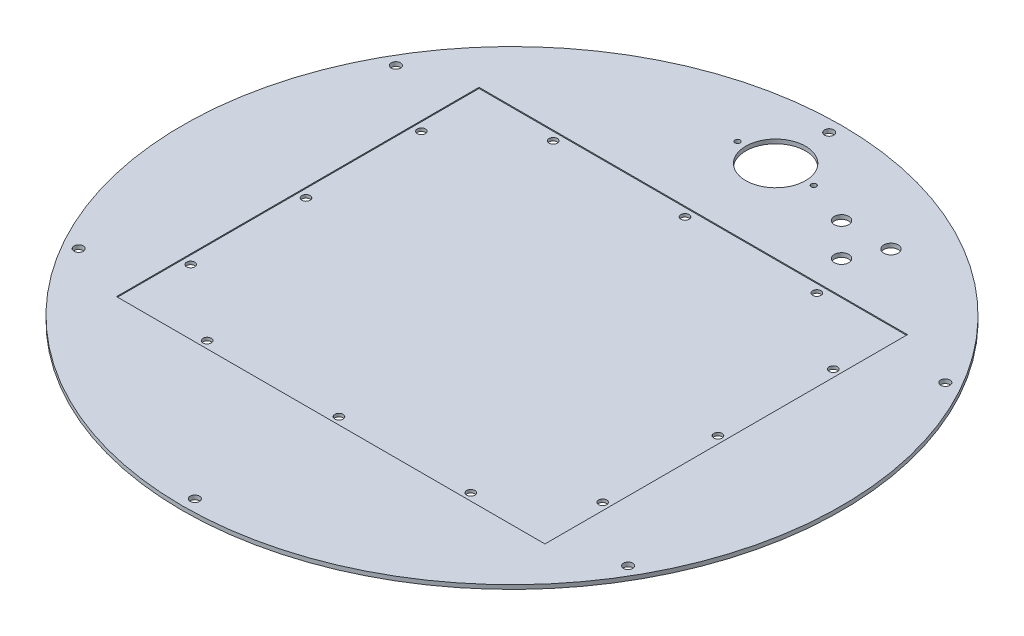
SolidWorks part; units mm, degrees
other " "
material "ASTM A36 Steel"
ref_plane "Front Plane" through (0, 0, 0) normal (0, 0, 1) x (1, 0, 0)
ref_plane "Top Plane" through (0, 0, 0) normal (0, 1, 0) x (1, 0, 0)
ref_plane "Right Plane" through (0, 0, 0) normal (1, 0, 0) x (0, 0, -1)
sketch "Sketch1" plane through (0, 0, 0) normal (0, 1, 0) x (1, 0, 0)
  circle A0 centre (0, 0) radius 508
  dimension "O.D." = 1016
extrude "Cover" add sketch "Sketch1" against normal blind 6.35
hole_wizard "Cover B.C." positions "Sketch17" profile "Sketch16" hole size "9/16" standard "Ansi Inch" end condition through all
sketch "Sketch17" plane through (0, 0, 0) normal (0, 1, 0) x (-1, 0, 0)
  point P1 (0, -488.95)
  point P14 (-423.4431, -244.475)
  point P15 (-423.4431, 244.475)
  point P16 (0, 488.95)
  point P17 (423.4431, 244.475)
  point P18 (423.4431, -244.475)
  dimension "coverB.C.rad" = 488.95
sketch "Sketch16" plane through (0, 0, -488.95) normal (1, 0, 0) x (0, 0, 1)
  line L0 (0, 0) -> (0, 6.35)
  line L1 (0, 6.35) -> (7.1437, 6.35)
  line L2 (7.1437, 6.35) -> (7.1437, 0)
  line L5 (7.1437, 0) -> (0, 0)
  line L11 (0, -6.35) -> (0, 107.95) construction
  dimension "Thru Hole Dia." = 14.2875
  dimension "Thru Hole Depth" = 6.35
sketch "Sketch3" plane through (0, 0, 0) normal (0, 1, 0) x (-1, 0, 0)
  line L1 (330.2, -279.4) -> (-330.2, -279.4)
  line L2 (330.2, -279.4) -> (330.2, 279.4)
  line L3 (330.2, 279.4) -> (-330.2, 279.4)
  line L4 (-330.2, -279.4) -> (-330.2, 279.4)
  dimension "hatchX" = 660.4
  dimension "hatchZ" = 558.8
  dimension "hatchXoffset" = 330.2
  dimension "hatchZoffset" = 279.4
extrude "Cover Hatch" cut sketch "Sketch3" against normal blind 1.5875
hole_wizard "Cover Hatch Bolt Holes" positions "Sketch47" profile "Sketch48" hole size "1/2" standard "ANSI Inch" end condition through all
sketch "Sketch47" plane through (0, -1.5875, 0) normal (0, 1, 0) x (1, 0, 0)
  line L0 (-330.2, 0) -> (330.2, 0) construction
  line L1 (-330.2, 279.4) -> (-330.2, -279.4) construction
  line L2 (330.2, -279.4) -> (330.2, 279.4) construction
  line L4 (0, 279.4) -> (0, -279.4) construction
  line L5 (330.2, 279.4) -> (-330.2, 279.4) construction
  line L6 (-330.2, -279.4) -> (330.2, -279.4) construction
  point P0 (-317.5, 177.8)
  point P2 (-317.5, 0)
  point P21 (-317.5, -177.8)
  point P23 (317.5, -177.8)
  point P24 (317.5, 0)
  point P25 (317.5, 177.8)
  point P26 (-203.2, 266.7)
  point P28 (0, 266.7)
  point P35 (203.2, 266.7)
  point P36 (203.2, -266.7)
  point P37 (0, -266.7)
  point P38 (-203.2, -266.7)
  dimension "hatchXinsetZ" = 12.7
  dimension "coverHatchZaxisBoltZinset" = 101.6
  dimension "hatchZinsetX" = 12.7
  dimension "coverHatchXaxisBoltXinset" = 127
sketch "Sketch48" plane through (-317.5, -1.5875, -177.8) normal (1, 0, 0) x (0, 0, 1)
  line L0 (0, 0) -> (0, 4.7625)
  line L1 (0, 4.7625) -> (6.35, 4.7625)
  line L2 (6.35, 4.7625) -> (6.35, 0)
  line L5 (6.35, 0) -> (0, 0)
  line L11 (0, -6.35) -> (0, 107.95) construction
  dimension "Thru Hole Dia." = 12.7
  dimension "Thru Hole Depth" = 4.7625
sketch "Sketch33" plane through (0, 0, 0) normal (0, 1, 0) x (1, 0, 0)
  circle A0 centre (0, 406.4) radius 46.0375
  dimension "coverHoleOneDia" = 92.075
  dimension "coverHoleOneXoffset" = 0
  dimension "coverHoleOneZoffset" = 406.4
extrude "Cover Hole One" cut sketch "Sketch33" against normal through all
hole_wizard "Cover Hole One B.C." positions "Sketch51" profile "Sketch52" hole size "3/8" standard "ANSI Inch" end condition through all
sketch "Sketch51" plane through (0, 0, 0) normal (0, 1, 0) x (1, 0, 0)
  line L0 (-46.0375, 406.4) -> (46.0375, 406.4) construction
  line L2 (0, 452.4375) -> (0, 360.3625) construction
  circle A0 centre (0, 406.4) radius 46.0375 construction
  point P0 (-58.7375, 406.4)
  point P13 (58.7375, 406.4)
  dimension "coverHoleOneB.C.OffsetRad" = 58.7375
sketch "Sketch52" plane through (-58.7375, 0, -406.4) normal (1, 0, 0) x (0, 0, 1)
  line L0 (0, 0) -> (0, 6.35)
  line L1 (0, 6.35) -> (3.9687, 6.35)
  line L2 (3.9687, 6.35) -> (3.9687, 0)
  line L5 (3.9687, 0) -> (0, 0)
  line L11 (0, -6.35) -> (0, 107.95) construction
  dimension "Thru Hole Dia." = 7.9375
  dimension "Thru Hole Depth" = 6.35
sketch "Sketch57" plane through (0, 0, 0) normal (0, 1, 0) x (1, 0, 0)
  circle A0 centre (177.8, 609.6) radius 46.0375
  dimension "coverHoleTwoDia" = 92.075
  dimension "coverHoleTwoXoffset" = 177.8
  dimension "coverHoleTwoZoffset" = 609.6
extrude "Cover Hole Two" [suppressed] cut sketch "Sketch57" against normal through all
hole_wizard "Cover Hole Two B.C." [suppressed] positions "Sketch58" profile "Sketch59" hole size "7/16" standard "ANSI Inch"
sketch "Sketch58" [suppressed] plane through (0, 0, 0) normal (0, 1, 0) x (1, 0, 0)
  line L2 (131.7625, 609.6) -> (223.8375, 609.6) construction
  line L4 (177.8, 655.6375) -> (177.8, 563.5625) construction
  circle A0 centre (177.8, 609.6) radius 46.0375 construction
  point P0 (119.0625, 609.6)
  point P17 (236.5375, 609.6)
  dimension "coverHoleTwoB.C.OffsetRad" = 58.7375
sketch "Sketch59" plane through (119.0625, 0, -609.6) normal (1, 0, 0) x (0, 0, 1)
  line L0 (0, 0) -> (0, 6.35)
  line L1 (0, 6.35) -> (3.9687, 6.35)
  line L2 (3.9687, 6.35) -> (3.9687, 0)
  line L5 (3.9687, 0) -> (0, 0)
  line L11 (0, -6.35) -> (0, 107.95) construction
  dimension "Thru Hole Dia." = 7.9375
  dimension "Thru Hole Depth" = 6.35
sketch "Sketch60" plane through (0, 0, 0) normal (0, 1, 0) x (1, 0, 0)
  circle A0 centre (431.8, 609.6) radius 46.0375
  dimension "coverHoleThreeDia" = 92.075
  dimension "coverHoleThreeXoffset" = 431.8
  dimension "coverHoleThreeZoffset" = 609.6
extrude "Cover Hole Three" [suppressed] cut sketch "Sketch60" against normal through all
hole_wizard "Cover Hole Three B.C." [suppressed] positions "Sketch61" profile "Sketch62" hole size "7/16" standard "ANSI Inch"
sketch "Sketch61" [suppressed] plane through (0, 0, 0) normal (0, 1, 0) x (1, 0, 0)
  line L0 (431.8, 655.6375) -> (431.8, 563.5625) construction
  line L2 (385.7625, 609.6) -> (477.8375, 609.6) construction
  circle A0 centre (431.8, 609.6) radius 46.0375 construction
  point P0 (373.0625, 609.6)
  point P14 (490.5375, 609.6)
  dimension "coverHoleThreeB.C.OffsetRad" = 58.7375
sketch "Sketch62" plane through (373.0625, 0, -609.6) normal (1, 0, 0) x (0, 0, 1)
  line L0 (0, 0) -> (0, 6.35)
  line L1 (0, 6.35) -> (3.9687, 6.35)
  line L2 (3.9687, 6.35) -> (3.9687, 0)
  line L5 (3.9687, 0) -> (0, 0)
  line L11 (0, -6.35) -> (0, 107.95) construction
  dimension "Thru Hole Dia." = 7.9375
  dimension "Thru Hole Depth" = 6.35
sketch "Sketch63" plane through (0, 0, 0) normal (0, 1, 0) x (1, 0, 0)
  circle A0 centre (584.2, 558.8) radius 11.1125
  dimension "coverHoleFourDia" = 22.225
  dimension "coverHoleFourXoffset" = 584.2
  dimension "coverHoleFourZoffset" = 558.8
extrude "Cover Hole Four" [suppressed] cut sketch "Sketch63" against normal through all
sketch "Sketch64" plane through (0, 0, 0) normal (0, 1, 0) x (1, 0, 0)
  circle A0 centre (508, 508) radius 11.1125
  dimension "coverHoleFiveDia" = 22.225
  dimension "coverHoleFiveXoffset" = 508
  dimension "coverHoleFiveZoffset" = 508
extrude "Cover Hole Five" [suppressed] cut sketch "Sketch64" against normal through all
sketch "Sketch Cover I.D. Outline" plane through (0, 0, 0) normal (0, 1, 0) x (1, 0, 0)
  circle A0 centre (0, 0) radius 457.2
  dimension "sketchCoverIDoutline" = 914.4
sketch "Sketch65" plane through (0, 0, 0) normal (0, 1, 0) x (1, 0, 0)
  circle A0 centre (127, 381) radius 11.1125
  dimension "coverHoleSixeDia" = 22.225
  dimension "coverHoleSixXoffset" = 127
  dimension "coverHoleSixZoffset" = 381
extrude "Cover Hole Six" cut sketch "Sketch65" against normal through all
sketch "Sketch66" plane through (0, 0, 0) normal (0, 1, 0) x (1, 0, 0)
  circle A0 centre (203.2, 381) radius 11.1125
  dimension "coverHoleSevenDia" = 22.225
  dimension "coverHoleSevenXoffset" = 203.2
  dimension "coverHoleSevenZoffset" = 381
extrude "Cover Hole Seven" cut sketch "Sketch66" against normal through all
sketch "Sketch67" plane through (0, 0, 0) normal (0, 1, 0) x (1, 0, 0)
  circle A0 centre (177.8, 330.2) radius 11.1125
  dimension "coverHoleEightDia" = 22.225
  dimension "coverHoleEightXoffset" = 177.8
  dimension "coverHoleEightZoffset" = 330.2
extrude "Cover Hole Eight" cut sketch "Sketch67" against normal through all
sketch "Sketch68" plane through (0, 0, 0) normal (0, 1, 0) x (1, 0, 0)
  line L0 (-508, 0) -> (508, 0) construction
  line L1 (0, 508) -> (0, -508) construction
  line L2 (-508, 177.8) -> (508, 177.8)
  line L3 (-508, -508) -> (508, -508)
  line L4 (508, -508) -> (508, 177.8)
  line L5 (-508, 177.8) -> (-508, -508)
  circle A0 centre (0, 0) radius 508 construction
  point P10 (21.4535, -508)
  point P12 (0, 177.8)
  point P15 (0, -508)
  dimension "FMcoverSplitZoffset" = 177.8
  dimension "FMcoverSplitXlength" = 1016
extrude "Split Cover FM A" [suppressed] cut sketch "Sketch68" against normal through all
sketch "Sketch69" plane through (0, 0, 0) normal (0, 1, 0) x (1, 0, 0)
  line L0 (-508, 0) -> (508, 0) construction
  line L1 (0, 508) -> (0, -508) construction
  line L2 (508, 508) -> (-508, 508)
  line L3 (-508, 508) -> (-508, 177.8)
  line L4 (-508, 177.8) -> (508, 177.8)
  line L5 (508, 177.8) -> (508, 508)
  circle A0 centre (0, 0) radius 508 construction
  point P10 (0, 508)
  dimension "FMbCoverSplitXlength" = 1016
  dimension "FMbCoverSplitZoffset" = 177.8
extrude "Split Cover FM B" [suppressed] cut sketch "Sketch69" against normal through all
sketch "Sketch71" [suppressed] plane through (0, 0, 0) normal (0, 1, 0) x (1, 0, 0)
  line L0 (0, 457.2) -> (0, -457.2) construction
  line L1 (-475.8688, 177.8) -> (475.8688, 177.8) construction
  circle A1 centre (0, 0) radius 457.2 construction
  circle A2 centre (0, 165.1) radius 6.35
  circle A3 centre (254, 165.1) radius 6.35
  circle A4 centre (-254, 165.1) radius 6.35
  point P11 (-254, 165.1)
  dimension "D1" = 12.7
  dimension "D2" = 12.7
  dimension "FMbCoverSplitB.C.Xoffset" = 254
extrude "Split Cover FM B B.C." [suppressed] cut sketch "Sketch71" against normal through all
